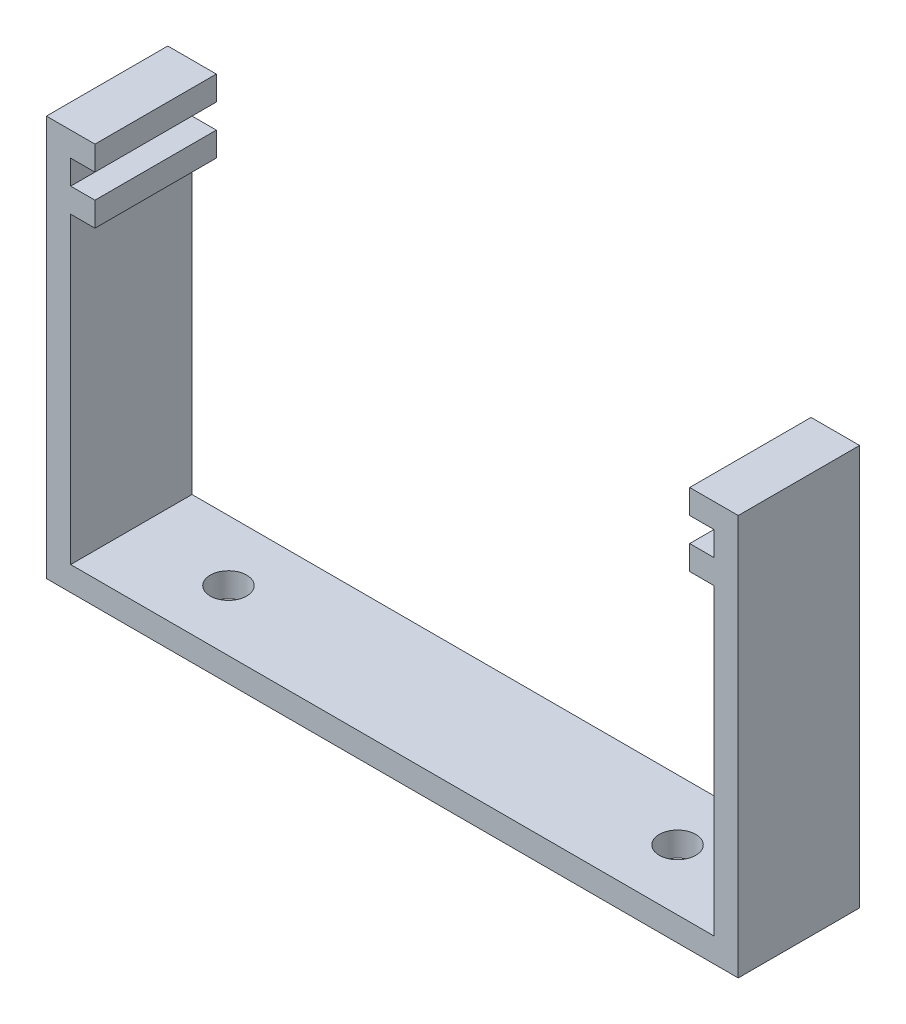
SolidWorks part; units mm, degrees
ref_plane "Alzado" through (0, 0, 0) normal (0, 0, 1) x (1, 0, 0)
ref_plane "Planta" through (0, 0, 0) normal (0, 1, 0) x (1, 0, 0)
ref_plane "Vista lateral" through (0, 0, 0) normal (1, 0, 0) x (0, 0, -1)
sketch "Croquis1" plane through (0, 0, 0) normal (0, 0, 1) x (1, 0, 0)
  line L0 (0, 0) -> (53, 0)
  line L1 (53, 0) -> (53, 25)
  line L2 (53, 25) -> (51, 25)
  line L3 (51, 25) -> (51, 27)
  line L4 (51, 27) -> (53, 27)
  line L5 (53, 27) -> (53, 29)
  line L6 (53, 29) -> (51, 29)
  line L7 (51, 29) -> (51, 31)
  line L8 (51, 31) -> (55, 31)
  line L9 (55, 31) -> (55, -2)
  line L10 (55, -2) -> (-2, -2)
  line L11 (26.5, 0) -> (26.5, 33.5121) construction
  line L13 (-2, 31) -> (-2, -2)
  line L14 (2, 31) -> (-2, 31)
  line L15 (2, 29) -> (2, 31)
  line L16 (0, 29) -> (2, 29)
  line L17 (0, 27) -> (0, 29)
  line L18 (2, 27) -> (0, 27)
  line L19 (2, 25) -> (2, 27)
  line L20 (0, 25) -> (2, 25)
  line L21 (0, 0) -> (0, 25)
  dimension "D1" = 53
  dimension "D2" = 25
  dimension "D3" = 2
  dimension "D4" = 2
  dimension "D5" = 2
  dimension "D6" = 2
  dimension "D7" = 4
  dimension "D8" = 2
extrude "Saliente-Extruir1" add sketch "Croquis1" along normal blind 10
sketch "Croquis2" plane through (0, -2, 0) normal (0, -1, 0) x (1, 0, 0)
  line L0 (55, 10) -> (55, 0) construction
  line L3 (-2, 10) -> (-2, 0) construction
  circle A0 centre (45, 5) radius 1.5
  circle A1 centre (8, 5) radius 1.5
  point P11 (0, 0)
  dimension "D1" = 3
  dimension "D3" = 3
  dimension "D2" = 10
  dimension "D4" = 10
extrude "Cortar-Extruir1" cut sketch "Croquis2" against normal blind 10
